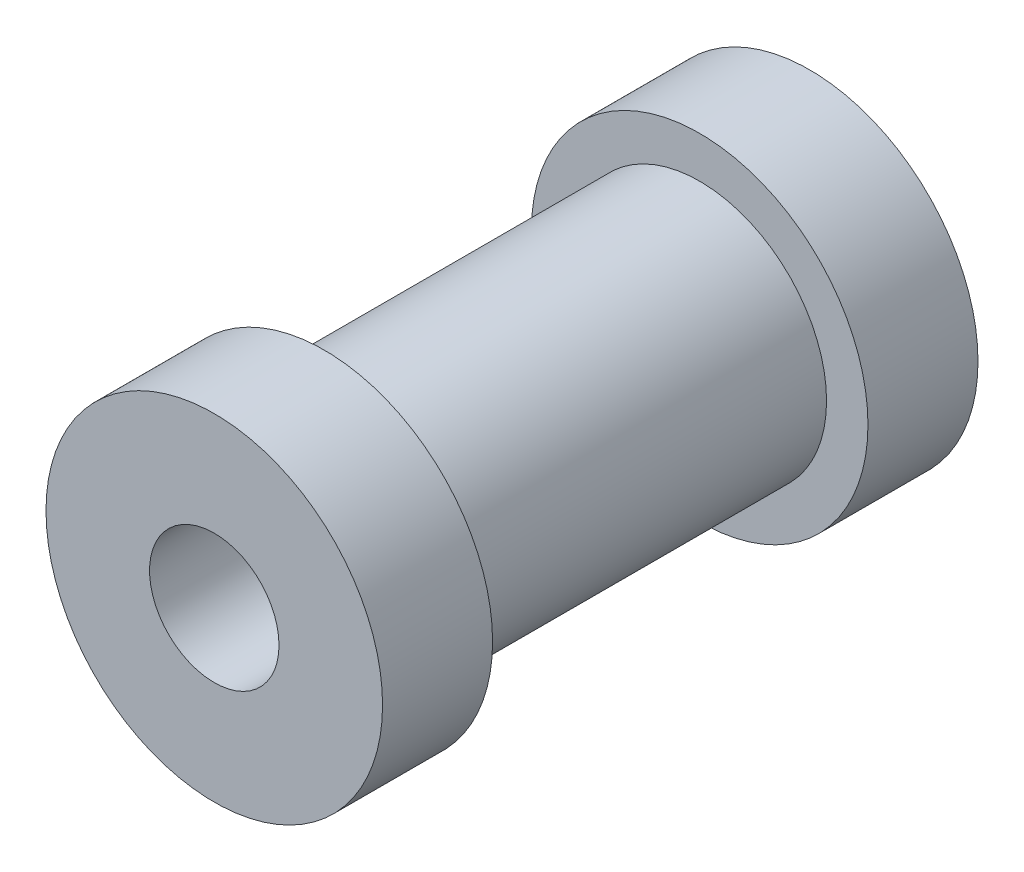
SolidWorks part; units mm, degrees
material "AISI 1020"
ref_plane "Спереди" through (0, 0, 0) normal (0, 0, 1) x (1, 0, 0)
ref_plane "Сверху" through (0, 0, 0) normal (0, 1, 0) x (1, 0, 0)
ref_plane "Справа" through (0, 0, 0) normal (1, 0, 0) x (0, 0, -1)
sketch "Эскиз2" plane through (0, 0, 0) normal (1, 0, 0) x (0, 0, -1)
  line L0 (-1000, 0) -> (49000, 0) construction
  line L1 (18.75, 0) -> (-4.25, 0)
  line L2 (-4.25, 0) -> (-4.25, 6.5)
  line L3 (-4.25, 6.5) -> (0, 6.5)
  line L4 (0, 6.5) -> (0, 4.9)
  line L5 (0, 4.9) -> (18.75, 4.9)
  line L6 (18.75, 4.9) -> (18.75, 0)
  line L7 (4, 5) -> (0, 5) construction
  line L8 (-4.25, 6.7493) -> (-4.25, -8.1951) construction
  line L9 (0, 8.2977) -> (0, -9.7154) construction
  line L10 (7.25, -23.3669) -> (7.25, 16.4809) construction
  point P15 (7.25, 0)
  dimension "D1" = 0.1
  dimension "D2" = 13
revolve "Повернуть1" add sketch "Эскиз2" angle 360 about L0
sketch "Эскиз3" plane through (0, 0, 0) normal (1, 0, 0) x (0, 0, -1)
  line L0 (-1000, 0) -> (49000, 0) construction
  line L2 (18.75, 6.5) -> (14.5, 6.5)
  line L3 (18.75, 6.5) -> (18.75, 4.9)
  line L4 (18.75, 4.9) -> (14.5, 4.9)
  line L5 (14.5, 6.5) -> (14.5, 4.9)
  line L6 (18.75, 4.9) -> (0, 4.9) construction
  line L7 (0, 6.5) -> (-4.25, 6.5) construction
  line L10 (18.75, 6.7493) -> (18.75, -8.1951) construction
revolve "Повернуть2" add sketch "Эскиз3" angle 360 about L0
hole_wizard "Отверстие обработанное метчиком M61" positions "Эскиз4" profile "Эскиз5" tap size "M6" standard "ISO"
sketch "Эскиз4" plane through (0, 0, 4.25) normal (0, 0, 1) x (1, 0, 0)
  point P0 (0, 0)
sketch "Эскиз5" plane through (0, 0, 4.25) normal (1, 0, 0) x (0, -1, 0)
  line L0 (0, 0) -> (0, 18.5022)
  line L1 (0, 18.5022) -> (2.5, 17)
  line L2 (2.5, 17) -> (2.5, 0)
  line L5 (2.5, 0) -> (0, 0)
  line L10 (0, 18.5022) -> (-2.5, 17) construction
  line L11 (0, -6.35) -> (0, 107.95) construction
  dimension "Диаметр сверла" = 5
  dimension "Глубина сверла" = 17
  dimension "Угол заточки сверла" = 118
cosmetic thread "Отверстие резьбы1" parameters "D1"=12, "D2"=6
hole_wizard "Отверстие обработанное метчиком M62" positions "Эскиз6" profile "Эскиз7" tap size "M6" standard "ISO"
sketch "Эскиз6" plane through (0, 0, -18.75) normal (0, 0, -1) x (-1, 0, 0)
  point P0 (0, 0)
sketch "Эскиз7" plane through (0, 0, -18.75) normal (1, 0, 0) x (0, 1, 0)
  line L0 (0, 0) -> (0, 18.5022)
  line L1 (0, 18.5022) -> (2.5, 17)
  line L2 (2.5, 17) -> (2.5, 0)
  line L5 (2.5, 0) -> (0, 0)
  line L10 (0, 18.5022) -> (-2.5, 17) construction
  line L11 (0, -6.35) -> (0, 107.95) construction
  dimension "Диаметр сверла" = 5
  dimension "Глубина сверла" = 17
  dimension "Угол заточки сверла" = 118
cosmetic thread "Отверстие резьбы2" parameters "D1"=12, "D2"=6
other "Сохранить тела1"
